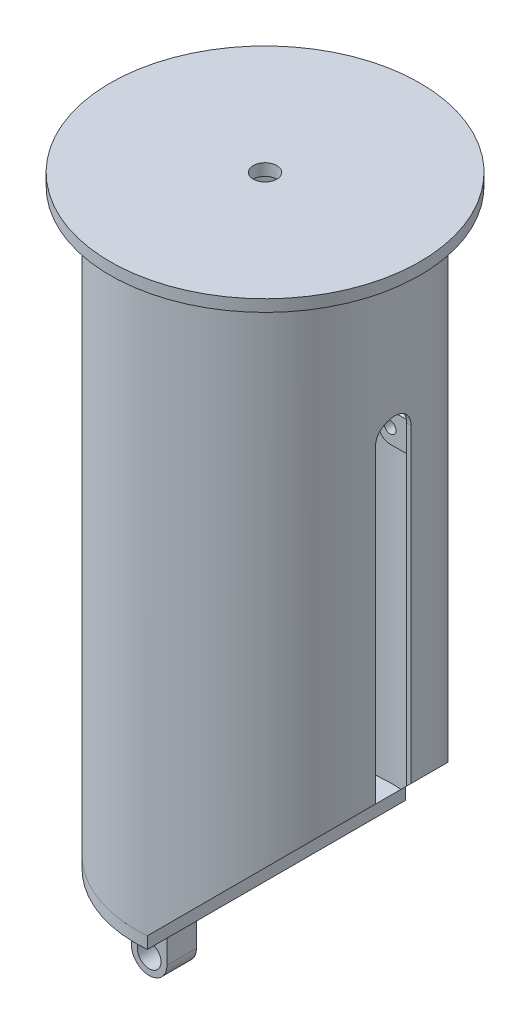
SolidWorks part; units mm, degrees
ref_plane "Plano frontal" through (0, 0, 0) normal (0, 0, 1) x (1, 0, 0)
ref_plane "Plano superior" through (0, 0, 0) normal (0, 1, 0) x (1, 0, 0)
ref_plane "Plano direito" through (0, 0, 0) normal (1, 0, 0) x (0, 0, -1)
sketch "Esboço1" plane through (0, 0, 0) normal (0, 0, 1) x (1, 0, 0)
  line L0 (0, 0) -> (0, 500) construction
  line L1 (0, 0) -> (215.8131, 0) construction
  line L2 (10, 500) -> (131, 500)
  line L3 (131, 500) -> (131, 490)
  line L4 (105.78, 0) -> (109.54, 0)
  line L7 (105.78, 0) -> (105.78, 490)
  line L8 (105.78, 490) -> (10, 490)
  line L10 (131, 490) -> (109.54, 490)
  line L11 (109.54, 490) -> (109.54, 0)
  line L12 (10, 500) -> (10, 490)
  dimension "D1" = 3.76
  dimension "D2" = 10
  dimension "D5" = 262
  dimension "D6" = 490
  dimension "D7" = 219.08
  dimension "D8" = 20
revolve "Revolução1" add sketch "Esboço1" angle 360 about L0
sketch "Esboço2" plane through (0, 0, 0) normal (0, 0, 1) x (1, 0, 0)
  line L0 (9.54, 0) -> (109.54, 100)
  line L1 (-109.54, 0) -> (109.54, 0) construction
  line L2 (109.54, 0) -> (109.54, 490) construction
  line L3 (109.54, 100) -> (109.54, 0)
  line L4 (109.54, 0) -> (9.54, 0)
  dimension "D1" = 45
  dimension "D2" = 100
extrude "Corte-extrusão1" cut sketch "Esboço2" against normal through all both and the other way through all
sketch "Esboço3" plane through (0, 0, 0) normal (0, -1, 0) x (1, 0, 0)
  line L0 (9.54, 109.1238) -> (9.54, -109.1238)
  arc A0 (9.54, 109.1238) -> (9.54, -109.1238) centre (0, 0) ccw construction
  arc A1 (9.54, 109.1238) -> (9.54, -109.1238) centre (0, 0) ccw
extrude "Ressalto-extrusão1" add sketch "Esboço3" along normal blind 10 separate body
sketch "Esboço4" plane through (0, 0, 0) normal (0, 0, 1) x (1, 0, 0)
  line L0 (-85.54, -10) -> (-85.54, -73.4941) construction
  line L1 (-109.54, -10) -> (9.54, -10) construction
  line L2 (-100.54, -10) -> (-100.54, -110)
  line L3 (-100.54, -10) -> (-70.54, -10)
  line L4 (-70.54, -10) -> (-70.54, -110)
  arc A0 (-100.54, -110) -> (-70.54, -110) centre (-85.54, -110) ccw
  circle A1 centre (-85.54, -110) radius 10
  dimension "D1" = 20
  dimension "D2" = 30
  dimension "D3" = 100
  dimension "D4" = 24
extrude "Ressalto-extrusão2" add sketch "Esboço4" along normal mid plane 25
sketch "Esboço5" plane through (0, 0, 0) normal (0, 0, 1) x (1, 0, 0)
  line L0 (105.78, 358.74) -> (85.78, 358.74)
  line L2 (105.78, 96.24) -> (105.78, 490) construction
  line L3 (75.78, 348.74) -> (75.78, 343.74)
  line L4 (85.78, 333.74) -> (105.78, 333.74)
  line L5 (105.78, 333.74) -> (105.78, 358.74)
  circle A0 centre (85.78, 346.24) radius 5
  arc A1 (75.78, 343.74) -> (85.78, 333.74) centre (85.78, 343.74) ccw
  arc A2 (85.78, 358.74) -> (75.78, 348.74) centre (85.78, 348.74) ccw
  point P8 (75.78, 346.24)
  point P11 (75.78, 333.74)
  point P14 (75.78, 358.74)
  dimension "D4" = 10
  dimension "D6" = 10
  dimension "D1" = 30
  dimension "D2" = 20
  dimension "D3" = 25
  dimension "D5" = 250
extrude "Ressalto-extrusão3" add sketch "Esboço5" along normal blind 8 from offset 20
mirror "Espelhar1" about plane through (0, 0, 0) normal (0, 0, 1) of "Ressalto-extrusão3"
sketch "Esboço6" plane through (0, 0, 0) normal (1, 0, 0) x (0, 0, -1)
  line L0 (0, 361.24) -> (0, 15) construction
  line L1 (15, 361.24) -> (15, 15)
  line L2 (-15, 361.24) -> (-15, 15)
  line L3 (-28, 346.24) -> (28, 346.24) construction
  line L4 (-28, 333.74) -> (-28, 358.74) construction
  line L5 (28, 358.74) -> (28, 333.74) construction
  line L6 (109.1238, 0) -> (-109.1238, 0) construction
  arc A0 (15, 361.24) -> (-15, 361.24) centre (0, 361.24) ccw
  arc A1 (-15, 15) -> (15, 15) centre (0, 15) ccw
  point P3 (0, 188.12)
  dimension "D1" = 15
  dimension "D2" = 30
extrude "Corte-extrusão2" cut sketch "Esboço6" along normal through all
